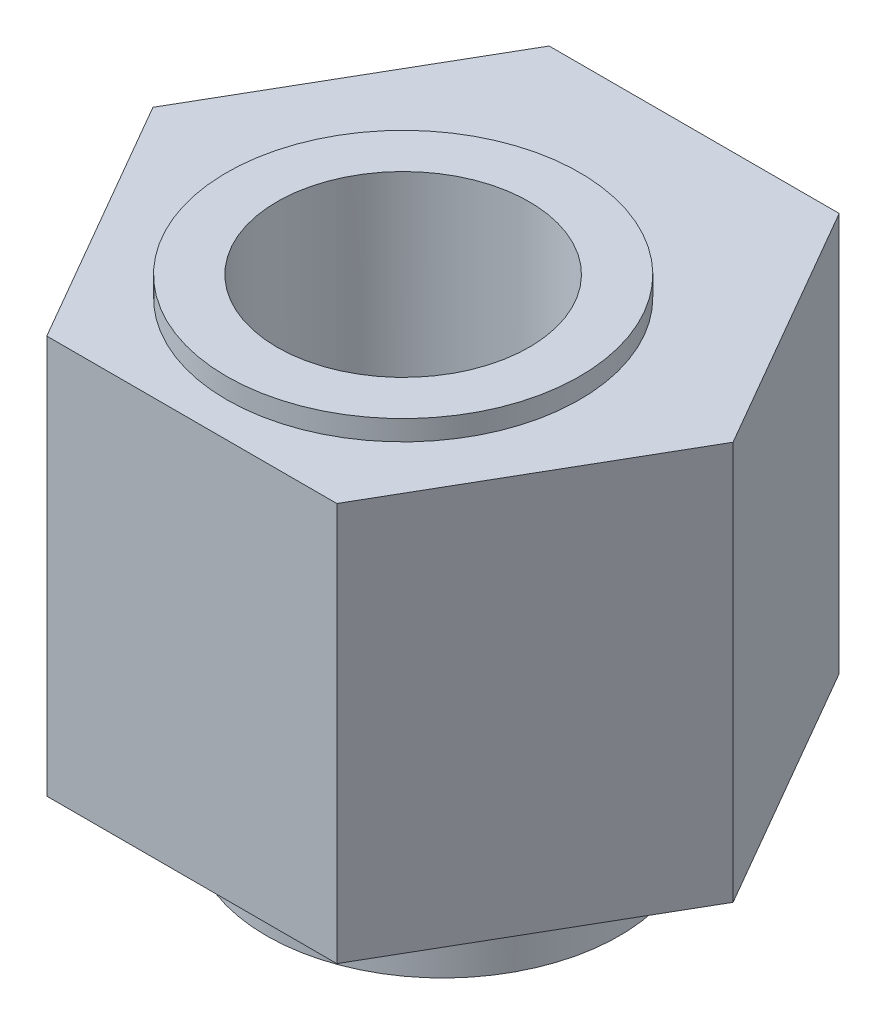
SolidWorks part; units mm, degrees
material "AISI 304"
ref_plane "Front Plane" through (0, 0, 0) normal (0, 0, 1) x (1, 0, 0)
ref_plane "Top Plane" through (0, 0, 0) normal (0, 1, 0) x (1, 0, 0)
ref_plane "Right Plane" through (0, 0, 0) normal (1, 0, 0) x (0, 0, -1)
sketch "Sketch1" plane through (0, 0, 0) normal (0, 1, 0) x (1, 0, 0)
  line L1 (5.7504, 0) -> (2.8752, 4.98)
  line L2 (2.8752, 4.98) -> (-2.8752, 4.98)
  line L3 (-2.8752, 4.98) -> (-5.7504, 0)
  line L4 (-5.7504, 0) -> (-2.8752, -4.98)
  line L5 (-2.8752, -4.98) -> (2.8752, -4.98)
  line L6 (2.8752, -4.98) -> (5.7504, 0)
  circle A0 centre (0, 0) radius 4.98 construction
  dimension "D1" = 9.96
extrude "Boss-Extrude1" add sketch "Sketch1" along normal blind 7.9
sketch "Sketch4" plane through (0, 7.9, 0) normal (0, 1, 0) x (1, 0, 0)
  line L0 (0, 0) -> (0, -0.79) construction
  circle A0 centre (0, -0.79) radius 2.5
  dimension "D1" = 5
  dimension "D2" = 0.79
extrude "Cut-Extrude1" cut sketch "Sketch4" against normal through all
sketch "草图1" plane through (0, 7.9, 0) normal (0, 1, 0) x (1, 0, 0)
  circle A0 centre (0, -0.79) radius 2.5
  circle A1 centre (0, -0.79) radius 3.5
  dimension "D1" = 7
extrude "凸台-拉伸1" add sketch "草图1" along normal blind 0.4
sketch "草图2" plane through (0, 0, 0) normal (0, -1, 0) x (1, 0, 0)
  circle A0 centre (0, 0) radius 3.5
  circle A1 centre (0, 0.79) radius 2.5
  dimension "D1" = 7
extrude "凸台-拉伸2" add sketch "草图2" along normal blind 1.7
